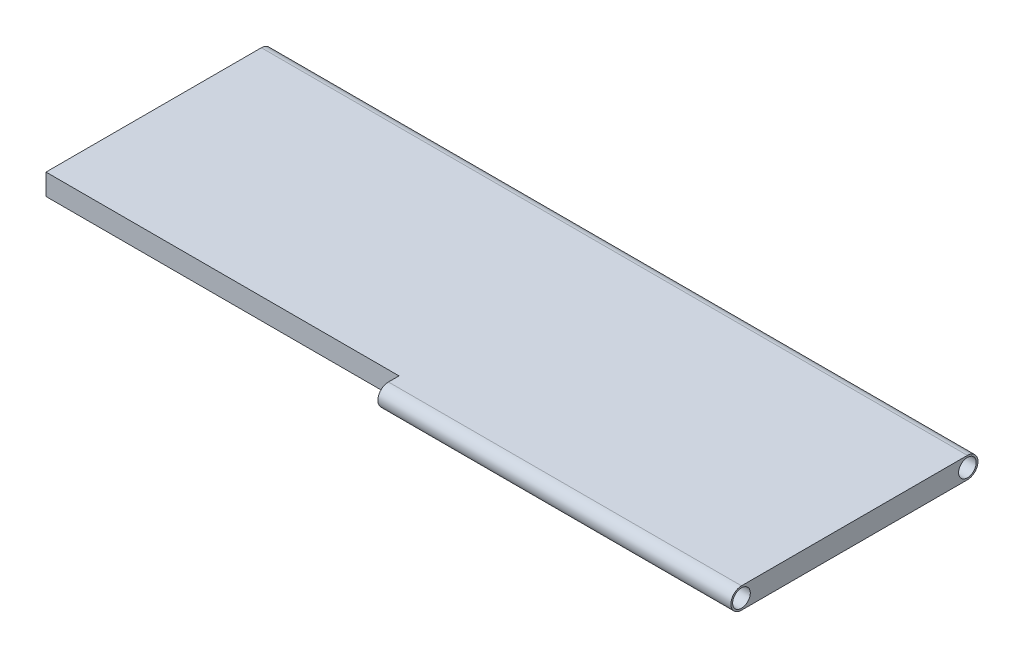
SolidWorks part; units mm, degrees
ref_plane "Front Plane" through (0, 0, 0) normal (0, 0, 1) x (1, 0, 0)
ref_plane "Top Plane" through (0, 0, 0) normal (0, 1, 0) x (1, 0, 0)
ref_plane "Right Plane" through (0, 0, 0) normal (1, 0, 0) x (0, 0, -1)
sketch "Sketch1" plane through (0, 0, 0) normal (0, 1, 0) x (1, 0, 0)
  line L1 (-500, 145) -> (500, 145)
  line L2 (-500, 145) -> (-500, -145)
  line L3 (-500, -145) -> (500, -145)
  line L4 (500, 145) -> (500, -145)
  line L5 (-500, 145) -> (500, -145) construction
  line L6 (-500, -145) -> (500, 145) construction
  point P0 (0, 0)
  dimension "D1" = 1000
  dimension "D2" = 290
extrude "Boss-Extrude1" add sketch "Sketch1" along normal blind 30
sketch "Sketch2" plane through (500, 0, 0) normal (1, 0, 0) x (0, 0, -1)
  line L0 (-145, 30) -> (-145, 0) construction
  line L1 (-160, 30) -> (-117.0675, 30)
  line L2 (-160, 0) -> (-117.0675, 0)
  circle A0 centre (-160, 15) radius 15
  circle A1 centre (-160, 15) radius 12.5
  point P4 (-145, 15)
  line M4 (-145, 30) -> (-145, 0)
  dimension "D1" = 30
  dimension "D2" = 25
extrude "Boss-Extrude2" add sketch "Sketch2" against normal blind 500 contours A0 L1 M4 | A0 L2 M4 | A0 A1
sketch "Sketch3" plane through (500, 0, 0) normal (1, 0, 0) x (0, 0, -1)
  line L0 (145, 30) -> (145, 0) construction
  line L1 (160, 30) -> (135.4412, 30)
  line L2 (160, 0) -> (135.4412, 0)
  circle A0 centre (160, 15) radius 15
  circle A1 centre (160, 15) radius 12.5
  point P5 (145, 15)
  line M3 (145, 0) -> (145, 30)
  dimension "D1" = 30
  dimension "D2" = 25
extrude "Boss-Extrude3" add sketch "Sketch3" against normal blind 1000 contours A0 L1 M3 | A0 A1 | A0 L2 M3
